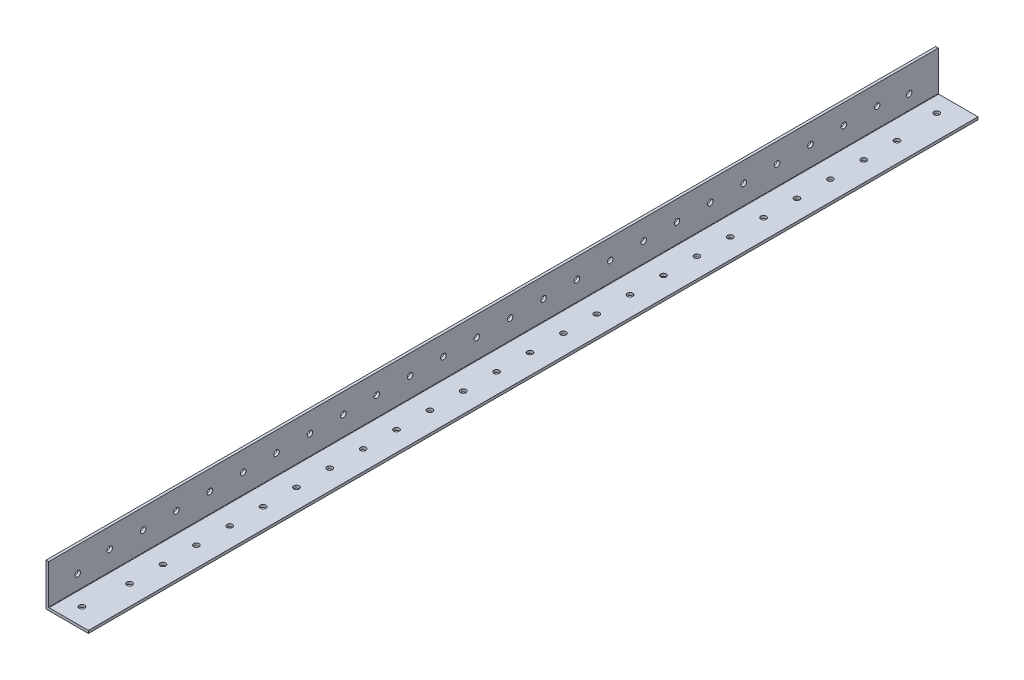
SolidWorks part; units mm, degrees
material "6061 Alloy"
ref_plane "Front Plane" through (0, 0, 0) normal (0, 0, 1) x (1, 0, 0)
ref_plane "Top Plane" through (0, 0, 0) normal (0, 1, 0) x (1, 0, 0)
ref_plane "Right Plane" through (0, 0, 0) normal (1, 0, 0) x (0, 0, -1)
sketch "Sketch1" plane through (0, 0, 0) normal (0, 0, 1) x (1, 0, 0)
  line L0 (0, 25.4) -> (0, 0) construction
  line L1 (0, 0) -> (25.4, 0) construction
  line L2 (25.4, 0) -> (25.4, 1.5875) construction
  line L3 (25.4, 1.5875) -> (1.5875, 1.5875) construction
  line L4 (1.5875, 1.5875) -> (1.5875, 25.4) construction
  line L6 (1.5875, 25.4) -> (0, 25.4) construction
  arc A0 (1.5875, 1.8415) -> (1.8415, 1.5875) centre (1.8415, 1.8415) ccw construction
  point P4 (0, 0)
  dimension "Inside Corner Radius" = 0.254
  dimension "Outside Height" = 25.4
  dimension "Inside Height" = 23.8125
  dimension "Outside Width" = 25.4
  dimension "Inside Width" = 23.8125
  dimension "Wall Thickness" = 1.5875
  dimension "Shape" = 90
sketch "Sketch2" plane through (0, 0, 0) normal (1, 0, 0) x (0, 0, -1)
  line L0 (1219.2, 0) -> (-1219.2, 0) construction
  line L1 (-1219.2, 25.4) -> (-1219.2, 0) construction
  line L2 (1219.2, 25.4) -> (1219.2, 0) construction
  point P0 (-1189.99, 0)
  point P4 (0, 0)
  point P6 (1189.99, 0)
  dimension "D1" = 29.21
  dimension "D2" = 29.21
  dimension "D3" = 25.4
  dimension "Length" = 2438.4
sketch "Sketch3" plane through (0, 0, 0) normal (0, 0, 1) x (1, 0, 0)
  line L0 (1.5875, 25.4) -> (0, 25.4)
  line L1 (0, 25.4) -> (0, 0)
  line L2 (0, 0) -> (25.4, 0)
  line L3 (25.4, 0) -> (25.4, 1.5875)
  line L4 (25.4, 1.5875) -> (1.5875, 1.5875)
  line L5 (1.5875, 1.5875) -> (1.5875, 25.4)
extrude "Boss-Extrude1" add sketch "Sketch3" along normal mid plane 2438.4
fillet "Fillet1" radius 0.254 1 edges at (1.5875, 1.5875, 0)
sketch "Sketch4" plane through (0, 0, 0) normal (-1, 0, 0) x (0, 0, 1)
  line L0 (1219.2, 25.4) -> (1219.2, 0) construction
  line L1 (-1219.2, 0) -> (686, 0)
  line L2 (-1219.2, 0) -> (-1219.2, 74.9453)
  line L3 (-1219.2, 74.9453) -> (686, 74.9453)
  line L4 (686, 0) -> (686, 74.9453)
  dimension "D1" = 533.2
extrude "Cut-Extrude1" cut sketch "Sketch4" against normal blind 60
sketch "Sketch9" plane through (1.5875, 0, 0) normal (1, 0, 0) x (0, 0, -1)
  line L0 (-722.6, 1.5875) -> (-722.6, 25.4) construction
  line L1 (-1219.2, 1.5875) -> (-686, 1.5875) construction
  line L2 (-1219.2, 25.4) -> (-686, 25.4) construction
  line L3 (-703.4625, 10.3759) -> (-722.6, 10.3759) construction
  line L4 (-1182.6, 25.4) -> (-1182.6, 1.5875) construction
  line L5 (-1201.7375, 10.3759) -> (-1182.6, 10.3759) construction
  circle A0 centre (-1201.7375, 10.3759) radius 1.65
  circle A1 centre (-703.4625, 10.3759) radius 1.65
  circle A2 centre (-722.6, 13.4937) radius 1.65
  circle A3 centre (-742.6, 13.4937) radius 1.65
  circle A4 centre (-762.6, 13.4937) radius 1.65
  circle A5 centre (-782.6, 13.4937) radius 1.65
  circle A6 centre (-802.6, 13.4937) radius 1.65
  circle A7 centre (-822.6, 13.4937) radius 1.65
  circle A8 centre (-842.6, 13.4937) radius 1.65
  circle A9 centre (-862.6, 13.4937) radius 1.65
  circle A10 centre (-882.6, 13.4937) radius 1.65
  circle A11 centre (-902.6, 13.4937) radius 1.65
  circle A12 centre (-922.6, 13.4937) radius 1.65
  circle A13 centre (-942.6, 13.4937) radius 1.65
  circle A14 centre (-962.6, 13.4937) radius 1.65
  circle A15 centre (-982.6, 13.4937) radius 1.65
  circle A16 centre (-1002.6, 13.4937) radius 1.65
  circle A17 centre (-1022.6, 13.4937) radius 1.65
  circle A18 centre (-1042.6, 13.4937) radius 1.65
  circle A19 centre (-1062.6, 13.4937) radius 1.65
  circle A20 centre (-1082.6, 13.4937) radius 1.65
  circle A21 centre (-1102.6, 13.4937) radius 1.65
  circle A22 centre (-1122.6, 13.4937) radius 1.65
  circle A23 centre (-1142.6, 13.4937) radius 1.65
  circle A24 centre (-1162.6, 13.4937) radius 1.65
  circle A25 centre (-1182.6, 13.4937) radius 1.65
  dimension "D1" = 3.3
  dimension "D2" = 20
extrude "Cut-Extrude5" cut sketch "Sketch9" against normal blind 60
sketch "Sketch10" plane through (0, 1.5875, 0) normal (0, 1, 0) x (1, 0, 0)
  line L0 (25.4, -1182.6) -> (1.5875, -1182.6) construction
  line L1 (25.4, -1219.2) -> (25.4, -686) construction
  line L2 (1.5875, -1219.2) -> (1.5875, -686) construction
  line L3 (11.1125, -1208.7918) -> (11.1125, -1182.6) construction
  line L4 (11.1125, -696.4082) -> (25.4, -696.4082) construction
  line L5 (13.4937, -722.6) -> (13.4937, -696.4082) construction
  circle A0 centre (11.1125, -696.4082) radius 1.65
  circle A1 centre (11.1125, -1208.7918) radius 1.65
  circle A2 centre (13.4938, -1182.6) radius 1.65
  circle A3 centre (13.4938, -1162.6) radius 1.65
  circle A4 centre (13.4938, -1142.6) radius 1.65
  circle A5 centre (13.4938, -1122.6) radius 1.65
  circle A6 centre (13.4938, -1102.6) radius 1.65
  circle A7 centre (13.4938, -1082.6) radius 1.65
  circle A8 centre (13.4938, -1062.6) radius 1.65
  circle A9 centre (13.4938, -1042.6) radius 1.65
  circle A10 centre (13.4938, -1022.6) radius 1.65
  circle A11 centre (13.4938, -1002.6) radius 1.65
  circle A12 centre (13.4938, -982.6) radius 1.65
  circle A13 centre (13.4938, -962.6) radius 1.65
  circle A14 centre (13.4938, -942.6) radius 1.65
  circle A15 centre (13.4938, -922.6) radius 1.65
  circle A16 centre (13.4938, -902.6) radius 1.65
  circle A17 centre (13.4938, -882.6) radius 1.65
  circle A18 centre (13.4938, -862.6) radius 1.65
  circle A19 centre (13.4938, -842.6) radius 1.65
  circle A20 centre (13.4938, -822.6) radius 1.65
  circle A21 centre (13.4938, -802.6) radius 1.65
  circle A22 centre (13.4938, -782.6) radius 1.65
  circle A23 centre (13.4938, -762.6) radius 1.65
  circle A24 centre (13.4938, -742.6) radius 1.65
  circle A25 centre (13.4937, -722.6) radius 1.65
  dimension "D1" = 3.3
  dimension "D3" = 20
  dimension "D2" = 24
extrude "Cut-Extrude6" cut sketch "Sketch10" against normal blind 60
equation "\"D1@Boss-Extrude1\"=\"Length@Sketch2\""
equation "\"D1@Sketch2\" = \"Outside Width@Sketch1\" * 1.15"
equation "\"D2@Sketch2\"=\"D1@Sketch2\""
equation "\"D1@Fillet1\"=\"Inside Corner Radius@Sketch1\""
equation "\"D3@Sketch2\"=\"Outside Height@Sketch1\""
